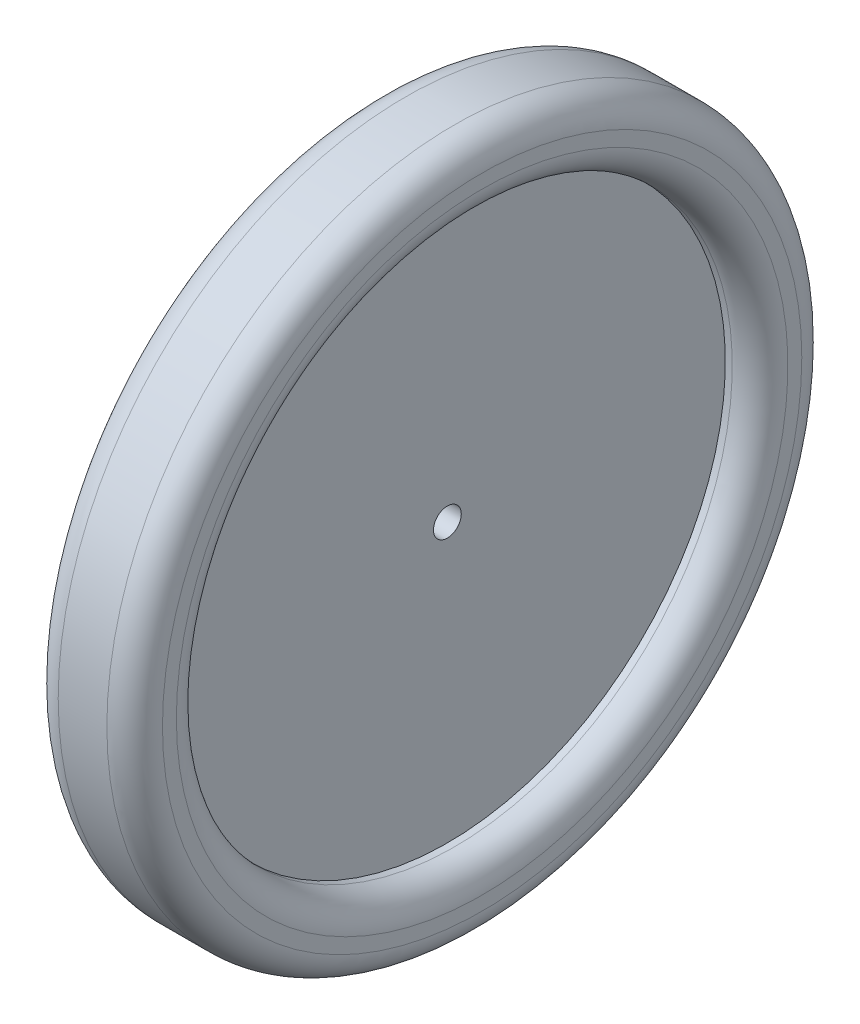
SolidWorks part; units mm, degrees
material "ABS"
ref_plane "Front Plane" through (0, 0, 0) normal (0, 0, 1) x (1, 0, 0)
ref_plane "Top Plane" through (0, 0, 0) normal (0, 1, 0) x (1, 0, 0)
ref_plane "Right Plane" through (0, 0, 0) normal (1, 0, 0) x (0, 0, -1)
sketch "Sketch2" plane through (0, 0, 0) normal (0, 0, 1) x (1, 0, 0)
  line L0 (0, 0) -> (0, 12.7) construction
  line L1 (0.889, 12.7) -> (-0.889, 12.7)
  line L2 (-1.905, 11.684) -> (-1.905, 11.176)
  line L3 (-0.889, 10.16) -> (-0.635, 10.16)
  line L4 (-0.635, 10.16) -> (-0.635, 0)
  line L5 (-0.635, 0) -> (0.635, 0)
  line L6 (0.635, 10.16) -> (0.635, 0)
  line L7 (0.889, 10.16) -> (0.635, 10.16)
  line L8 (1.905, 11.684) -> (1.905, 11.176)
  arc A0 (-1.905, 11.176) -> (-0.889, 10.16) centre (-0.889, 11.176) ccw
  arc A1 (-0.889, 12.7) -> (-1.905, 11.684) centre (-0.889, 11.684) ccw
  arc A2 (0.889, 12.7) -> (1.905, 11.684) centre (0.889, 11.684) cw
  arc A3 (1.905, 11.176) -> (0.889, 10.16) centre (0.889, 11.176) cw
  point P10 (-1.905, 10.16)
  point P13 (-1.905, 12.7)
  dimension "D5" = 1.016
  dimension "D1" = 12.7
  dimension "D2" = 10.16
  dimension "D3" = 1.27
  dimension "D4" = 3.81
revolve "Revolve1" add sketch "Sketch2" angle 360 about L5
sketch "Sketch3" plane through (0.635, 0, 0) normal (1, 0, 0) x (0, 0, -1)
  circle A0 centre (0, 0) radius 0.508
  dimension "D1" = 1.016
extrude "Cut-Extrude1" cut sketch "Sketch3" against normal through all
